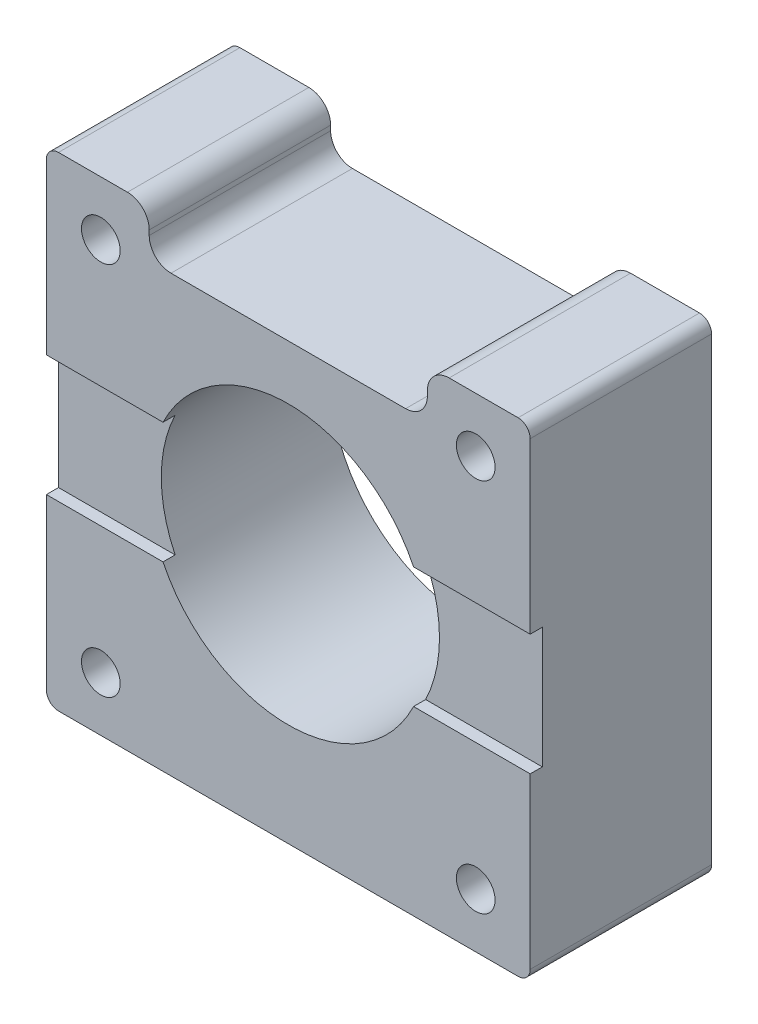
SolidWorks part; units mm, degrees
ref_plane "Front Plane" through (0, 0, 0) normal (0, 0, 1) x (1, 0, 0)
ref_plane "Top Plane" through (0, 0, 0) normal (0, 1, 0) x (1, 0, 0)
ref_plane "Right Plane" through (0, 0, 0) normal (1, 0, 0) x (0, 0, -1)
sketch "Sketch1" plane through (0, 0, 0) normal (0, 0, 1) x (1, 0, 0)
  line L0 (-20, 19) -> (-20, -19)
  line L1 (-15.5, -15.5) -> (15.5, -15.5) construction
  line L2 (-15.5, -15.5) -> (-15.5, 15.5) construction
  line L3 (-15.5, 15.5) -> (15.5, 15.5) construction
  line L4 (15.5, -15.5) -> (15.5, 15.5) construction
  line L5 (-15.5, -15.5) -> (15.5, 15.5) construction
  line L6 (-15.5, 15.5) -> (15.5, -15.5) construction
  line L7 (-19, -20) -> (19, -20)
  line L8 (20, 19) -> (20, -19)
  line L9 (-19, 20) -> (-13.3, 20)
  line L11 (-20, -20) -> (20, 20) construction
  line L12 (-20, 20) -> (20, -20) construction
  line L14 (13.3, 20) -> (19, 20)
  line L15 (-9.7, 16) -> (9.7, 16)
  line L16 (-11.5, 17.8) -> (-11.5, 18.2)
  line L18 (11.5, 17.8) -> (11.5, 18.2)
  circle A0 centre (0, 0) radius 11.5
  circle A1 centre (-15.5, 15.5) radius 1.6
  circle A2 centre (15.5, 15.5) radius 1.6
  circle A3 centre (15.5, -15.5) radius 1.6
  circle A4 centre (-15.5, -15.5) radius 1.6
  arc A5 (-20, -19) -> (-19, -20) centre (-19, -19) ccw
  arc A6 (19, -20) -> (20, -19) centre (19, -19) ccw
  arc A7 (20, 19) -> (19, 20) centre (19, 19) ccw
  arc A8 (-20, 19) -> (-19, 20) centre (-19, 19) cw
  arc A15 (-9.7, 16) -> (-11.5, 17.8) centre (-9.7, 17.8) cw
  arc A16 (11.5, 17.8) -> (9.7, 16) centre (9.7, 17.8) cw
  arc A17 (13.3, 20) -> (11.5, 18.2) centre (13.3, 18.2) ccw
  arc A18 (-13.3, 20) -> (-11.5, 18.2) centre (-13.3, 18.2) cw
  point P0 (0, 0)
  point P36 (-20, 6)
  point P43 (20, 6)
  point P44 (0, 20)
  dimension "D3" = 23
  dimension "D4" = 40
  dimension "D6" = 1
  dimension "D9" = 1.8
  dimension "D1" = 31
  dimension "D2" = 31
  dimension "D5" = 40
extrude "Boss-Extrude1" add sketch "Sketch1" along normal blind 15
sketch "Sketch2" plane through (0, 0, 15) normal (0, 0, 1) x (1, 0, 0)
  line L0 (20, -19) -> (20, 19) construction
  line L1 (-20, -5) -> (20, -5)
  line L2 (-20, -5) -> (-20, 5)
  line L3 (-20, 5) -> (20, 5)
  line L4 (20, -5) -> (20, 5)
  line L5 (-20, -5) -> (20, 5) construction
  line L6 (-20, 5) -> (20, -5) construction
  point P0 (0, 0)
  dimension "D1" = 10
extrude "Cut-Extrude1" cut sketch "Sketch2" against normal blind 1
